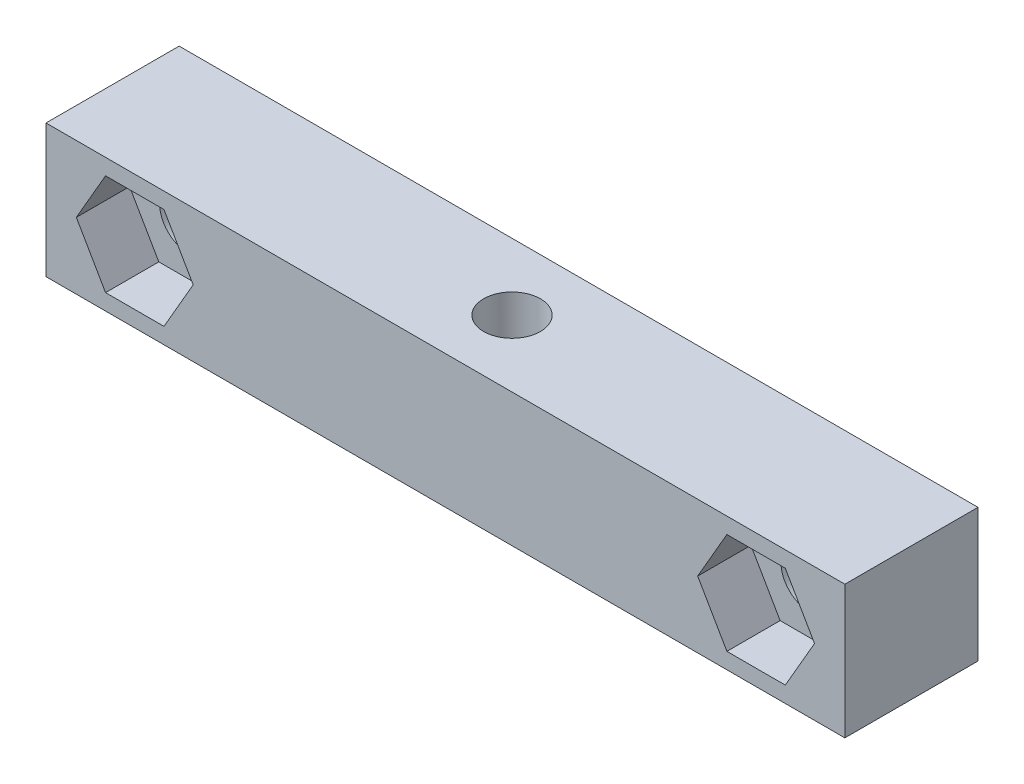
SolidWorks part; units mm, degrees
ref_plane "Alzado" through (0, 0, 0) normal (0, 0, 1) x (1, 0, 0)
ref_plane "Planta" through (0, 0, 0) normal (0, 1, 0) x (1, 0, 0)
ref_plane "Vista lateral" through (0, 0, 0) normal (1, 0, 0) x (0, 0, -1)
sketch "Croquis1" plane through (0, 0, 0) normal (0, 0, 1) x (1, 0, 0)
  line L0 (-22.5, 0) -> (-17.5, 0) construction
  line L1 (22.5, -3.75) -> (-22.5, -3.75)
  line L2 (22.5, -3.75) -> (22.5, 3.75)
  line L3 (22.5, 3.75) -> (-22.5, 3.75)
  line L4 (-22.5, -3.75) -> (-22.5, 3.75)
  line L5 (22.5, -3.75) -> (-22.5, 3.75) construction
  line L6 (22.5, 3.75) -> (-22.5, -3.75) construction
  line L7 (-17.5, 0) -> (17.5, 0) construction
  line L8 (17.5, 0) -> (22.5, 0) construction
  circle A0 centre (-17.5, 0) radius 1.6
  circle A1 centre (17.5, 0) radius 1.6
  point P0 (0, 0)
  dimension "D1" = 3.2
  dimension "D2" = 7.5
  dimension "D3" = 45
  dimension "D4" = 35
extrude "Saliente-Extruir1" add sketch "Croquis1" along normal blind 7.5
sketch "Croquis2" plane through (0, 3.75, 0) normal (0, 1, 0) x (1, 0, 0)
  line L0 (22.5, -3.75) -> (-22.5, -3.75) construction
  line L1 (22.5, -7.5) -> (22.5, 0) construction
  line L2 (-22.5, -7.5) -> (-22.5, 0) construction
  circle A0 centre (0, -3.75) radius 1.6
  dimension "D1" = 3.2
extrude "Cortar-Extruir1" cut sketch "Croquis2" against normal up to next
sketch "Croquis3" plane through (0, -3.75, 0) normal (0, -1, 0) x (1, 0, 0)
  line L1 (3.2909, 3.75) -> (1.6454, 6.6)
  line L2 (1.6454, 6.6) -> (-1.6454, 6.6)
  line L3 (-1.6454, 6.6) -> (-3.2909, 3.75)
  line L4 (-3.2909, 3.75) -> (-1.6454, 0.9)
  line L5 (-1.6454, 0.9) -> (1.6454, 0.9)
  line L6 (1.6454, 0.9) -> (3.2909, 3.75)
  circle A0 centre (0, 3.75) radius 2.85 construction
  dimension "D1" = 5.7
extrude "Cortar-Extruir2" cut sketch "Croquis3" against normal blind 3
sketch "Croquis4" plane through (0, 0, 7.5) normal (0, 0, 1) x (1, 0, 0)
  line L1 (-14.2091, 0) -> (-15.8546, 2.85)
  line L2 (-15.8546, 2.85) -> (-19.1454, 2.85)
  line L3 (-19.1454, 2.85) -> (-20.7909, 0)
  line L4 (-20.7909, 0) -> (-19.1454, -2.85)
  line L5 (-19.1454, -2.85) -> (-15.8546, -2.85)
  line L6 (-15.8546, -2.85) -> (-14.2091, 0)
  line L7 (20.7909, 0) -> (19.1454, 2.85)
  line L8 (19.1454, 2.85) -> (15.8546, 2.85)
  line L9 (15.8546, 2.85) -> (14.2091, 0)
  line L10 (14.2091, 0) -> (15.8546, -2.85)
  line L11 (15.8546, -2.85) -> (19.1454, -2.85)
  line L12 (19.1454, -2.85) -> (20.7909, 0)
  circle A0 centre (-17.5, 0) radius 2.85 construction
  circle A1 centre (17.5, 0) radius 2.85 construction
  dimension "D1" = 5.7
extrude "Cortar-Extruir3" cut sketch "Croquis4" against normal blind 3
